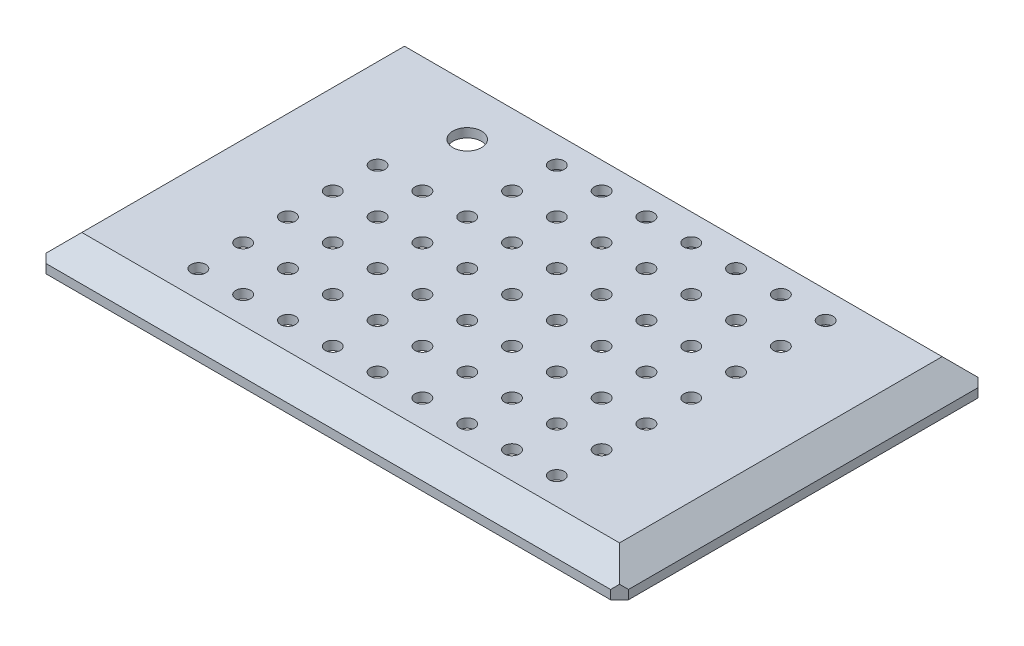
SolidWorks part; units mm, degrees
ref_plane "Front Plane" through (0, 0, 0) normal (0, 0, 1) x (1, 0, 0)
ref_plane "Top Plane" through (0, 0, 0) normal (0, 1, 0) x (1, 0, 0)
ref_plane "Right Plane" through (0, 0, 0) normal (1, 0, 0) x (0, 0, -1)
sketch "Sketch1" plane through (0, 0, 0) normal (0, 1, 0) x (1, 0, 0)
  line L1 (-65, -41) -> (65, -41)
  line L2 (-65, -41) -> (-65, 41)
  line L3 (-65, 41) -> (65, 41)
  line L4 (65, -41) -> (65, 41)
  line L5 (-65, -41) -> (65, 41) construction
  line L6 (-65, 41) -> (65, -41) construction
  point P0 (0, 0)
  dimension "D1" = 130
  dimension "D2" = 82
extrude "Boss-Extrude1" add sketch "Sketch1" along normal blind 2
sketch "Sketch2" plane through (0, 2, 0) normal (0, 1, 0) x (1, 0, 0)
  line L4 (65, -41) -> (65, 41)
  line L5 (65, 41) -> (-65, 41)
  line L6 (-65, 41) -> (-65, -41)
  line L7 (-65, -41) -> (65, -41)
  line L8 (65, -41) -> (65, 41)
  line L9 (65, 41) -> (-65, 41)
  line L10 (-65, 41) -> (-65, -41)
  line L11 (-65, -41) -> (65, -41)
  dimension "D1" = 0
ref_plane "Plane1" through (0, 7, 0) normal (0, 1, 0) x (1, 0, 0)
sketch "Sketch3" plane through (0, 7, 0) normal (0, 1, 0) x (1, 0, 0)
  line L0 (-65, 41) -> (-65, -41) construction
  line L1 (-60, -36) -> (60, -36)
  line L2 (-60, -36) -> (-60, 36)
  line L3 (-60, 36) -> (60, 36)
  line L4 (60, -36) -> (60, 36)
  line L5 (-60, -36) -> (60, 36) construction
  line L6 (-60, 36) -> (60, -36) construction
  line L7 (65, 41) -> (-65, 41) construction
  point P0 (0, 0)
  dimension "D1" = 5
  dimension "D2" = 5
loft "Loft1" add profiles "Sketch3", "Sketch2"
chamfer "Chamfer2" distance 2 angle 45 4 edges at (65, 1, 41) (65, 1, -41) (-65, 1, -41) (-65, 1, 41)
sketch "Sketch4" plane through (0, 0, 0) normal (0, -1, 0) x (1, 0, 0)
  line L0 (-65, -39) -> (-65, 39) construction
  line L1 (-57.9, 15) -> (-49.9, 15)
  line L2 (-57.9, 15) -> (-57.9, 25)
  line L3 (-57.9, 25) -> (-49.9, 25)
  line L4 (-49.9, 15) -> (-49.9, 25)
  line L5 (-57.9, 15) -> (-49.9, 25) construction
  line L6 (-57.9, 25) -> (-49.9, 15) construction
  line L7 (-65, 0) -> (65, 0) construction
  line L8 (65, 39) -> (65, -39) construction
  line L9 (0, 41) -> (0, -41) construction
  line L10 (-63, 41) -> (63, 41) construction
  line L11 (63, -41) -> (-63, -41) construction
  line L12 (-57.9, -25) -> (-49.9, -15) construction
  line L13 (-57.9, -15) -> (-49.9, -25) construction
  line L14 (-49.9, -15) -> (-49.9, -25)
  line L15 (-57.9, -25) -> (-49.9, -25)
  line L16 (-57.9, -15) -> (-57.9, -25)
  line L17 (-57.9, -15) -> (-49.9, -15)
  line L18 (57.9, -15) -> (49.9, -25) construction
  line L19 (57.9, -25) -> (49.9, -15) construction
  line L20 (57.9, 25) -> (49.9, 15) construction
  line L21 (57.9, 15) -> (49.9, 25) construction
  line L22 (57.9, -15) -> (49.9, -15)
  line L23 (57.9, -15) -> (57.9, -25)
  line L24 (57.9, -25) -> (49.9, -25)
  line L25 (49.9, -15) -> (49.9, -25)
  line L26 (49.9, 15) -> (49.9, 25)
  line L27 (57.9, 25) -> (49.9, 25)
  line L28 (57.9, 15) -> (57.9, 25)
  line L29 (57.9, 15) -> (49.9, 15)
  point P0 (-53.9, 20)
  point P21 (-53.9, -20)
  point P30 (53.9, -20)
  point P31 (53.9, 20)
  dimension "D1" = 10
  dimension "D2" = 7.1
  dimension "D3" = 8
  dimension "D4" = 40
extrude "Boss-Extrude2" add sketch "Sketch4" along normal blind 7
sketch "Sketch5" plane through (-57.9, 0, 0) normal (-1, 0, 0) x (0, 0, 1)
  line L0 (-15, 0) -> (-25, -7) construction
  line L1 (0, 0) -> (0, 50000) construction
  circle A0 centre (-20, -3.5) radius 2.05
  circle A1 centre (20, -3.5) radius 2.05
  dimension "D1" = 4.1
extrude "Cut-Extrude1" cut sketch "Sketch5" against normal through all
sketch "Sketch6" plane through (0, 0, 0) normal (0, -1, 0) x (1, 0, 0)
  line L0 (49.9, 25) -> (49.9, 15) construction
  line L1 (-48.9, -35) -> (48.9, -35)
  line L2 (-48.9, -35) -> (-48.9, 35)
  line L3 (-48.9, 35) -> (48.9, 35)
  line L4 (48.9, -35) -> (48.9, 35)
  line L5 (-48.9, -35) -> (48.9, 35) construction
  line L6 (-48.9, 35) -> (48.9, -35) construction
  line L8 (-60, 36) -> (60, 36) construction
  point P0 (0, 0)
  dimension "D1" = 1
  dimension "D2" = 1
extrude "Cut-Extrude2" cut sketch "Sketch6" against normal offset from surface (5 mm away) 2 up to face at (0, 7, 0)
sketch "Sketch7" plane through (0, 5, 0) normal (0, -1, 0) x (1, 0, 0)
  line L0 (0, 35) -> (0, -35) construction
  line L1 (-48.9, 35) -> (48.9, 35) construction
  line L2 (-48.9, -35) -> (48.9, -35) construction
  line L3 (-48.9, 0) -> (48.9, 0) construction
  line L4 (-48.9, -35) -> (-48.9, 35) construction
  line L5 (48.9, 35) -> (48.9, -35) construction
  circle A0 centre (0, 0) radius 1.65
  circle A1 centre (10, 0) radius 1.65
  circle A2 centre (20, 0) radius 1.65
  circle A3 centre (30, 0) radius 1.65
  circle A4 centre (40, 0) radius 1.65
  circle A7 centre (10, 10) radius 1.65
  circle A8 centre (20, 10) radius 1.65
  circle A9 centre (30, 10) radius 1.65
  circle A10 centre (40, 10) radius 1.65
  circle A13 centre (10, 20) radius 1.65
  circle A14 centre (20, 20) radius 1.65
  circle A15 centre (30, 20) radius 1.65
  circle A16 centre (40, 20) radius 1.65
  circle A19 centre (10, 30) radius 1.65
  circle A20 centre (20, 30) radius 1.65
  circle A21 centre (30, 30) radius 1.65
  circle A22 centre (40, 30) radius 1.65
  circle A25 centre (0, 10) radius 1.65
  circle A26 centre (0, 20) radius 1.65
  circle A27 centre (0, 30) radius 1.65
  circle A36 centre (-40, 30) radius 1.65
  circle A37 centre (-30, 30) radius 1.65
  circle A38 centre (-20, 30) radius 1.65
  circle A39 centre (-10, 30) radius 1.65
  circle A41 centre (-40, 20) radius 1.65
  circle A42 centre (-30, 20) radius 1.65
  circle A43 centre (-20, 20) radius 1.65
  circle A44 centre (-10, 20) radius 1.65
  circle A46 centre (-40, 10) radius 1.65
  circle A47 centre (-30, 10) radius 1.65
  circle A48 centre (-20, 10) radius 1.65
  circle A49 centre (-10, 10) radius 1.65
  circle A51 centre (-40, 0) radius 1.65
  circle A52 centre (-30, 0) radius 1.65
  circle A53 centre (-20, 0) radius 1.65
  circle A54 centre (-10, 0) radius 1.65
  circle A55 centre (-10, -10) radius 1.65
  circle A56 centre (-20, -10) radius 1.65
  circle A57 centre (-30, -10) radius 1.65
  circle A58 centre (-40, -10) radius 1.65
  circle A60 centre (-10, -20) radius 1.65
  circle A61 centre (-20, -20) radius 1.65
  circle A62 centre (-30, -20) radius 1.65
  circle A63 centre (-40, -20) radius 1.65
  circle A65 centre (-10, -30) radius 1.65
  circle A66 centre (-20, -30) radius 1.65
  circle A67 centre (-30, -30) radius 1.65
  circle A68 centre (-40, -30) radius 1.65
  circle A70 centre (0, -30) radius 1.65
  circle A71 centre (0, -20) radius 1.65
  circle A72 centre (0, -10) radius 1.65
  circle A74 centre (40, -30) radius 1.65
  circle A75 centre (30, -30) radius 1.65
  circle A76 centre (20, -30) radius 1.65
  circle A77 centre (10, -30) radius 1.65
  circle A79 centre (40, -20) radius 1.65
  circle A80 centre (30, -20) radius 1.65
  circle A81 centre (20, -20) radius 1.65
  circle A82 centre (10, -20) radius 1.65
  circle A84 centre (40, -10) radius 1.65
  circle A85 centre (30, -10) radius 1.65
  circle A86 centre (20, -10) radius 1.65
  circle A87 centre (10, -10) radius 1.65
  dimension "D1" = 3.3
  dimension "D2" = 5
  dimension "D3" = 4
extrude "Cut-Extrude3" cut sketch "Sketch7" against normal through all
sketch "Sketch8" plane through (0, 7, 0) normal (0, 1, 0) x (1, 0, 0)
  line L0 (-40, 30) -> (-30, 20) construction
  line L1 (-30, 20) -> (-30, 30) construction
  line L2 (-30, 30) -> (-40, 20) construction
  circle A0 centre (-35, 25) radius 3.2
  dimension "D1" = 6.4
extrude "Cut-Extrude4" cut sketch "Sketch8" against normal through all
sketch "Sketch9" plane through (0, 7, 0) normal (0, 1, 0) x (1, 0, 0)
  circle A0 centre (-30, 20) radius 1.65 construction
  circle A1 centre (-40, 20) radius 1.65 construction
  circle A2 centre (-40, 30) radius 1.65 construction
  circle A3 centre (-30, 30) radius 1.65 construction
  circle A4 centre (-30, 20) radius 1.65
  circle A5 centre (-40, 20) radius 1.65
  circle A6 centre (-40, 30) radius 1.65
  circle A7 centre (-30, 30) radius 1.65
extrude "Boss-Extrude3" add sketch "Sketch9" against normal up to surface (2 mm away) up to face at (-35, 5, -28.2)
